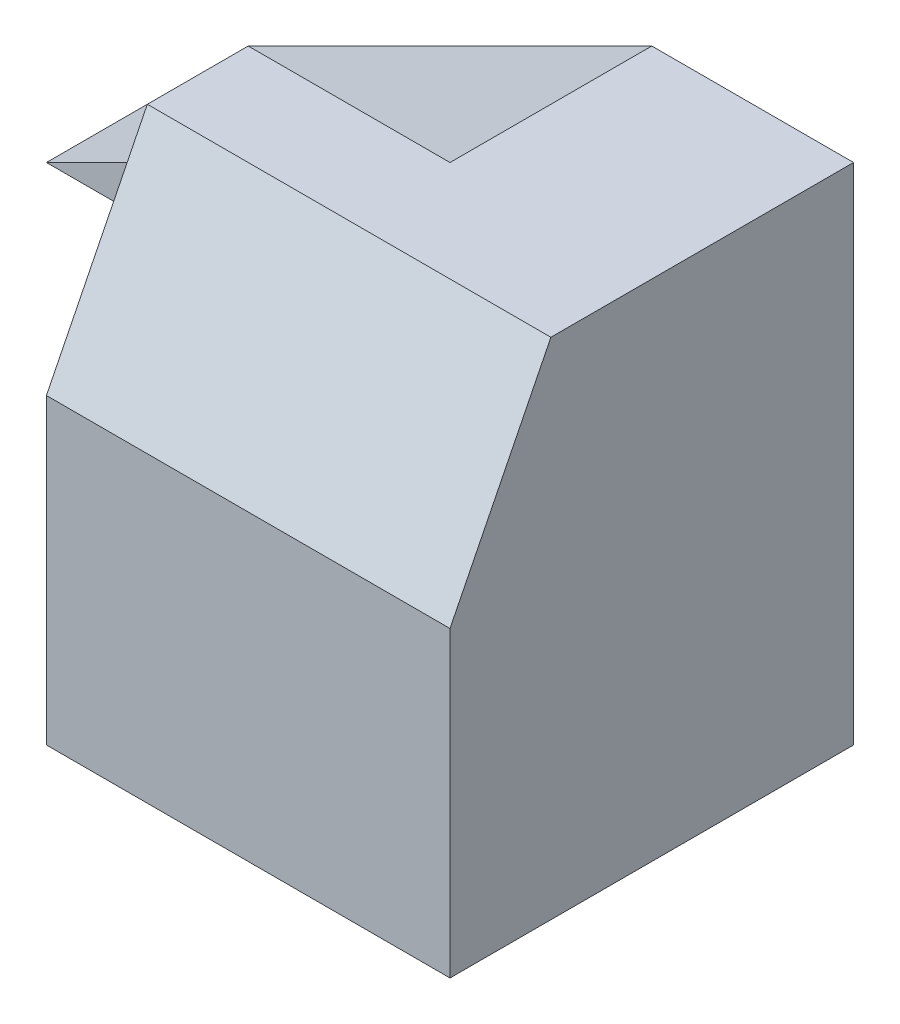
SolidWorks part; units mm, degrees
ref_plane "Front Plane" through (0, 0, 0) normal (0, 0, 1) x (1, 0, 0)
ref_plane "Top Plane" through (0, 0, 0) normal (0, 1, 0) x (1, 0, 0)
ref_plane "Right Plane" through (0, 0, 0) normal (1, 0, 0) x (0, 0, -1)
sketch "Sketch1" plane through (0, 0, 0) normal (0, 0, 1) x (1, 0, 0)
  line L1 (0, 0) -> (20, 0)
  line L2 (0, 0) -> (0, 25)
  line L3 (0, 25) -> (20, 25)
  line L4 (20, 0) -> (20, 25)
  dimension "D1" = 20
  dimension "D2" = 25
extrude "Boss-Extrude1" add sketch "Sketch1" along normal blind 20
sketch "Sketch3" plane through (0, 0, 0) normal (-1, 0, 0) x (0, 0, 1)
  line L0 (15, 25) -> (20, 15)
  line L1 (20, 25) -> (0, 25) construction
  line L2 (20, 25) -> (20, 0) construction
  line L3 (20, 15) -> (20, 25)
  line L4 (20, 25) -> (15, 25)
  dimension "D1" = 10
  dimension "D2" = 5
extrude "Cut-Extrude1" cut sketch "Sketch3" against normal blind 20
sketch "Sketch4" plane through (0, 0, 0) normal (-1, 0, 0) x (0, 0, 1)
  line L1 (0, 25) -> (10, 25)
  line L2 (0, 25) -> (0, 15)
  line L3 (0, 15) -> (10, 15)
  line L4 (10, 25) -> (10, 15)
  dimension "D1" = 10
  dimension "D2" = 10
extrude "Boss-Extrude2" add sketch "Sketch4" along normal blind 10
sketch "Sketch5" plane through (0, 0, 10) normal (0, 0, 1) x (1, 0, 0)
  line L0 (-10, 15) -> (10, 25)
  line L1 (20, 25) -> (0, 25) construction
  line L2 (10, 25) -> (-10, 25)
  line L3 (-10, 25) -> (-10, 15)
  dimension "D1" = 20
extrude "Cut-Extrude2" cut sketch "Sketch5" against normal blind 50
sketch "Sketch6" plane through (0, 0, 0) normal (0, -1, 0) x (1, 0, 0)
  line L0 (0, 10) -> (5, 0)
  line L1 (0, 20) -> (0, 0) construction
  line L2 (0, 0) -> (20, 0) construction
  line L3 (5, 0) -> (0, 0)
  line L4 (0, 0) -> (0, 10)
  dimension "D1" = 5
extrude "Cut-Extrude3" cut sketch "Sketch6" against normal blind 15
